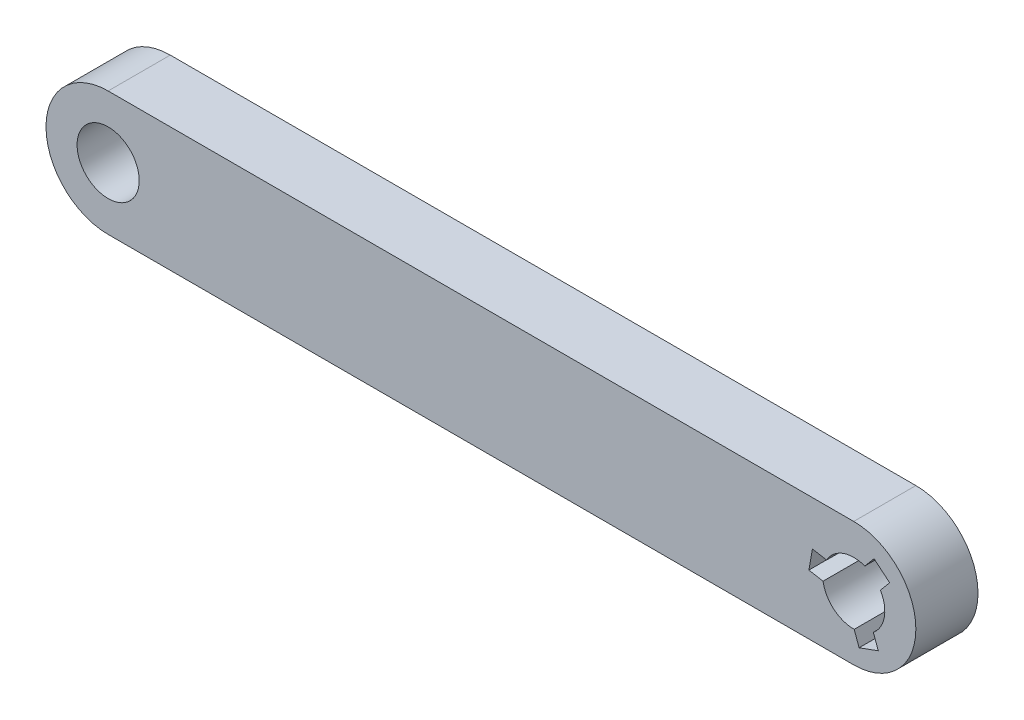
SolidWorks part; units mm, degrees
ref_plane "Front Plane" through (0, 0, 0) normal (0, 0, 1) x (1, 0, 0)
ref_plane "Top Plane" through (0, 0, 0) normal (0, 1, 0) x (1, 0, 0)
ref_plane "Right Plane" through (0, 0, 0) normal (1, 0, 0) x (0, 0, -1)
ref_plane "Plane4"
sketch "Sketch1" plane through (0, 0, 0) normal (0, 0, 1) x (1, 0, 0)
  line L0 (-76.2, -6.35) -> (0, -6.35)
  line L1 (0, 6.35) -> (-76.2, 6.35)
  line L2 (0.5504, -4.557) -> (0.0472, -3.1746)
  line L3 (-3.1346, -0.5047) -> (-4.5833, -0.2493)
  line L4 (-4.5833, -0.2493) -> (-4.4025, 0.7763)
  line L5 (-4.4025, 0.7763) -> (-4.2216, 1.8019)
  line L6 (-4.2216, 1.8019) -> (-2.7729, 1.5464)
  line L7 (1.1302, 2.967) -> (2.0758, 4.0939)
  line L8 (2.0758, 4.0939) -> (2.8735, 3.4245)
  line L9 (2.8735, 3.4245) -> (3.6713, 2.7551)
  line L10 (3.6713, 2.7551) -> (2.7257, 1.6282)
  line L11 (2.0044, -2.4623) -> (2.5076, -3.8446)
  line L12 (2.5076, -3.8446) -> (1.529, -4.2008)
  line L13 (1.529, -4.2008) -> (0.5504, -4.557)
  arc A0 (-76.2, 6.35) -> (-76.2, -6.35) centre (-76.2, 0) ccw
  arc A1 (0, -6.35) -> (0, 6.35) centre (0, 0) ccw
  circle A2 centre (-76.2, 0) radius 3.175
  arc A3 (-3.1346, -0.5047) -> (0.0472, -3.1746) centre (0, 0) ccw
  arc A4 (1.1302, 2.967) -> (-2.7729, 1.5464) centre (0, 0) ccw
  arc A5 (2.0044, -2.4623) -> (2.7257, 1.6282) centre (0, 0) ccw
  dimension "D4" = 12.7
  dimension "D7" = 6.35
  dimension "D1" = 4.4704
  dimension "D2" = 1.0414
  dimension "D3" = 1.0414
  dimension "D5" = 76.2
  dimension "D6" = 76.2
extrude "Extrusion1" add sketch "Sketch1" along normal blind 6.35 contours L0 A1 L1 A0 A5 L11 L12 L13 L2 A3 L3 L4 L5 L6 A4 L7 L8 L9 L10 A2
